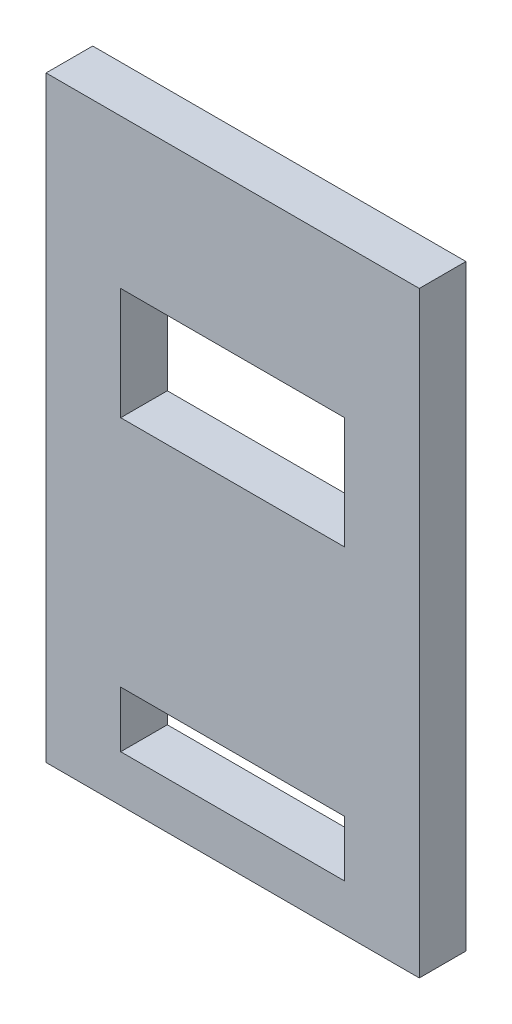
SolidWorks part; units mm, degrees
ref_plane "Front Plane" through (0, 0, 0) normal (0, 0, 1) x (1, 0, 0)
ref_plane "Top Plane" through (0, 0, 0) normal (0, 1, 0) x (1, 0, 0)
ref_plane "Right Plane" through (0, 0, 0) normal (1, 0, 0) x (0, 0, -1)
sketch "Sketch1" plane through (0, 0, 0) normal (0, 0, 1) x (1, 0, 0)
  line L1 (-42.7885, 106.0154) -> (84.2115, 106.0154)
  line L2 (-42.7885, 106.0154) -> (-42.7885, -97.1846)
  line L3 (-42.7885, -97.1846) -> (84.2115, -97.1846)
  line L4 (84.2115, 106.0154) -> (84.2115, -97.1846)
  dimension "D1" = 127
  dimension "D2" = 203.2
extrude "Boss-Extrude1" add sketch "Sketch1" along normal blind 15.875
sketch "Sketch2" plane through (0, 0, 15.875) normal (0, 0, 1) x (1, 0, 0)
  line L1 (20.7115, 17.1154) -> (20.7115, -62.2596) construction
  line L2 (20.7115, -62.2596) -> (20.7115, -97.1846) construction
  line L3 (-42.7885, -97.1846) -> (84.2115, -97.1846) construction
  line L5 (84.2115, -97.1846) -> (84.2115, 106.0154) construction
  line L7 (84.2115, 106.0154) -> (-42.7885, 106.0154) construction
  line L9 (-17.3885, 55.2154) -> (58.8115, 55.2154)
  line L10 (-17.3885, 55.2154) -> (-17.3885, 17.1154)
  line L11 (-17.3885, 17.1154) -> (58.8115, 17.1154)
  line L12 (58.8115, 55.2154) -> (58.8115, 17.1154)
  line L14 (-17.3885, -62.2596) -> (58.8115, -62.2596)
  line L15 (-17.3885, -62.2596) -> (-17.3885, -81.3096)
  line L16 (-17.3885, -81.3096) -> (58.8115, -81.3096)
  line L17 (58.8115, -62.2596) -> (58.8115, -81.3096)
  dimension "D2" = 168.275
  dimension "D3" = 50.8
  dimension "D4" = 38.1
  dimension "D5" = 76.2
  dimension "D7" = 25.4
  dimension "D8" = 19.05
  dimension "D9" = 76.2
  dimension "D11" = 25.4
extrude "Cut-Extrude2" cut sketch "Sketch2" against normal through all
